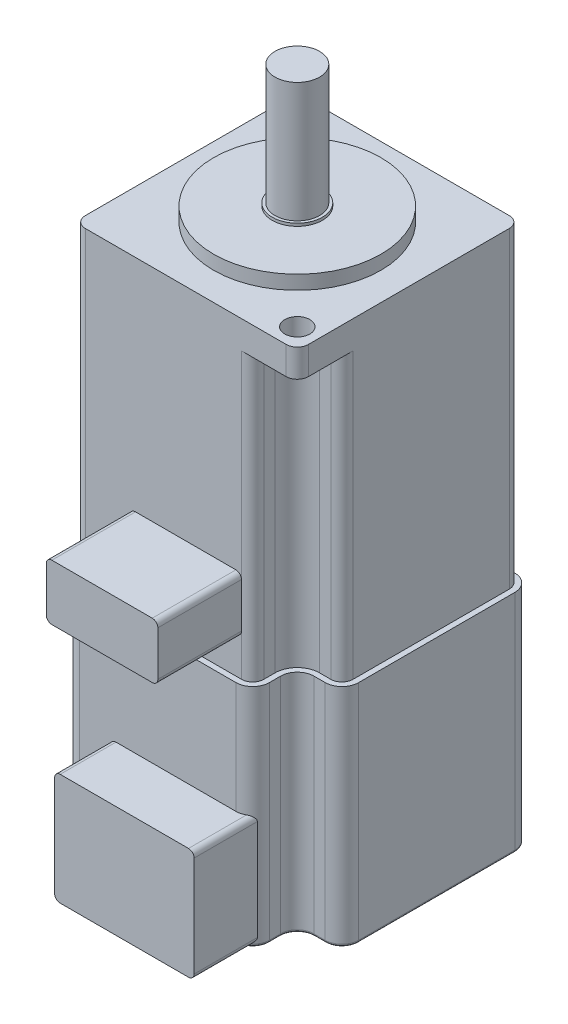
SolidWorks part; units mm, degrees
material "Ductile Iron"
ref_plane "Front Plane" through (0, 0, 0) normal (0, 0, 1) x (1, 0, 0)
ref_plane "Top Plane" through (0, 0, 0) normal (0, 1, 0) x (1, 0, 0)
ref_plane "Right Plane" through (0, 0, 0) normal (1, 0, 0) x (0, 0, -1)
sketch "Sketch1" plane through (0, 0, 0) normal (0, 1, 0) x (1, 0, 0)
  line L1 (2, 0) -> (38, 0)
  line L2 (0, 2) -> (0, 38)
  line L3 (2, 40) -> (38, 40)
  line L4 (40, 2) -> (40, 38)
  arc A0 (40, 38) -> (38, 40) centre (38, 38) ccw
  arc A1 (38, 0) -> (40, 2) centre (38, 2) ccw
  arc A2 (0, 2) -> (2, 0) centre (2, 2) ccw
  arc A3 (2, 40) -> (0, 38) centre (2, 38) ccw
  point P11 (0, 0)
  point P14 (0, 40)
  dimension "D2" = 2
  dimension "D1" = 40
extrude "Boss-Extrude1" add sketch "Sketch1" along normal blind 5
sketch "Sketch2" plane through (0, 5, 0) normal (0, 1, 0) x (1, 0, 0)
  line L0 (38, 40) -> (2, 40) construction
  line L1 (0, 38) -> (0, 2) construction
  circle A0 centre (20, 20) radius 15
  point P0 (20, 40)
  point P1 (0, 20)
  dimension "D1" = 30
extrude "Boss-Extrude2" add sketch "Sketch2" along normal blind 2.5
sketch "Sketch3" plane through (0, 5, 0) normal (0, 1, 0) x (1, 0, 0)
  line L0 (0.5858, 39.4142) -> (39.4142, 0.5858) construction
  circle A0 centre (20, 20) radius 23
  arc A1 (2, 40) -> (0, 38) centre (2, 38) ccw construction
  arc A2 (38, 0) -> (40, 2) centre (38, 2) ccw construction
  circle A3 centre (3.7365, 36.2635) radius 2.25
  circle A4 centre (36.2635, 3.7365) radius 2.25
  dimension "D1" = 46
  dimension "D2" = 4.5
  dimension "D3" = 4.5
extrude "Cut-Extrude1" cut sketch "Sketch3" against normal up to surface (5 mm away) contours A4 | A3 up to face at (20, 0, -20)
sketch "Sketch4" plane through (0, 0, 0) normal (0, -1, 0) x (1, 0, 0)
  line L0 (32, -2) -> (32, -4)
  line L1 (2, 0) -> (30, 0)
  line L2 (0, -2) -> (0, -30)
  line L3 (10, -40) -> (38, -40)
  line L4 (40, -10) -> (40, -38)
  line L5 (36, -8) -> (38, -8)
  line L6 (40, -2) -> (40, -38) construction
  line L7 (2, -32) -> (4, -32)
  line L8 (8, -36) -> (8, -38)
  arc A0 (40, -38) -> (38, -40) centre (38, -38) cw
  arc A1 (2, 0) -> (0, -2) centre (2, -2) ccw
  arc A2 (10, -40) -> (8, -38) centre (10, -38) cw
  arc A3 (2, -32) -> (0, -30) centre (2, -30) cw
  arc A4 (40, -10) -> (38, -8) centre (38, -10) ccw
  arc A5 (32, -2) -> (30, 0) centre (30, -2) ccw
  arc A6 (36, -8) -> (32, -4) centre (36, -4) cw
  arc A7 (4, -32) -> (8, -36) centre (4, -36) cw
  point P9 (0, 0)
  point P18 (8, -40)
  point P21 (0, -32)
  point P24 (40, -8)
  point P27 (32, 0)
  point P30 (32, -8)
  point P33 (8, -32)
  dimension "D2" = 2
  dimension "D1" = 2
  dimension "D7" = 4
  dimension "D3" = 8
  dimension "D4" = 8
  dimension "D5" = 8
  dimension "D6" = 8
extrude "Boss-Extrude3" add sketch "Sketch4" along normal blind 51
sketch "Sketch5" plane through (0, -51, 0) normal (0, -1, 0) x (1, 0, 0)
  line L16 (10, -41) -> (38, -41)
  line L17 (41, -38) -> (41, -10)
  line L18 (38, -7) -> (36, -7)
  line L19 (33, -4) -> (33, -2)
  line L20 (30, 1) -> (2, 1)
  line L21 (-1, -2) -> (-1, -30)
  line L22 (2, -33) -> (4, -33)
  line L23 (7, -36) -> (7, -38)
  line L24 (10, -41) -> (38, -41)
  line L25 (41, -38) -> (41, -10)
  line L26 (38, -7) -> (36, -7)
  line L27 (33, -4) -> (33, -2)
  line L28 (30, 1) -> (2, 1)
  line L29 (-1, -2) -> (-1, -30)
  line L30 (2, -33) -> (4, -33)
  line L31 (7, -36) -> (7, -38)
  arc A16 (7, -38) -> (10, -41) centre (10, -38) ccw
  arc A17 (38, -41) -> (41, -38) centre (38, -38) ccw
  arc A18 (41, -10) -> (38, -7) centre (38, -10) ccw
  arc A19 (33, -4) -> (36, -7) centre (36, -4) ccw
  arc A20 (33, -2) -> (30, 1) centre (30, -2) ccw
  arc A21 (2, 1) -> (-1, -2) centre (2, -2) ccw
  arc A22 (-1, -30) -> (2, -33) centre (2, -30) ccw
  arc A23 (7, -36) -> (4, -33) centre (4, -36) ccw
  arc A24 (7, -38) -> (10, -41) centre (10, -38) ccw
  arc A25 (38, -41) -> (41, -38) centre (38, -38) ccw
  arc A26 (41, -10) -> (38, -7) centre (38, -10) ccw
  arc A27 (33, -4) -> (36, -7) centre (36, -4) ccw
  arc A28 (33, -2) -> (30, 1) centre (30, -2) ccw
  arc A29 (2, 1) -> (-1, -2) centre (2, -2) ccw
  arc A30 (-1, -30) -> (2, -33) centre (2, -30) ccw
  arc A31 (7, -36) -> (4, -33) centre (4, -36) ccw
  dimension "D1" = 1
extrude "Boss-Extrude4" add sketch "Sketch5" along normal blind 40.5
sketch "Sketch6" plane through (0, 7.5, 0) normal (0, 1, 0) x (1, 0, 0)
  circle A0 centre (20, 20) radius 4.5
  dimension "D1" = 9
extrude "Boss-Extrude5" add sketch "Sketch6" along normal blind 0.5
sketch "Sketch7" plane through (0, 8, 0) normal (0, 1, 0) x (1, 0, 0)
  circle A0 centre (20, 20) radius 4
  dimension "D1" = 8
extrude "Boss-Extrude6" add sketch "Sketch7" along normal blind 21.5
fillet "Fillet1" radius 0.5 16 edges at (7, -91.5, -37) (6.1213, -91.5, -33.8787) (3, -91.5, -33) (-0.1213, -91.5, -32.1213) (-1, -91.5, -16) (-0.1213, -91.5, 0.1213) (16, -91.5, 1) (32.1213, -91.5, 0.1213) (33, -91.5, -3) (33.8787, -91.5, -6.1213) (37, -91.5, -7) (40.1213, -91.5, -7.8787) (41, -91.5, -24) (40.1213, -91.5, -40.1213) (24, -91.5, -41) (7.8787, -91.5, -40.1213)
sketch "Sketch8" plane through (0, 0, 0) normal (0, 0, 1) x (1, 0, 0)
  line L0 (20, 5) -> (20, -159.8867) construction
  line L1 (2, 5) -> (38, 5) construction
  line L3 (11, -34.5) -> (29, -34.5)
  line L4 (10, -35.5) -> (10, -43.5)
  line L5 (11, -44.5) -> (29, -44.5)
  line L6 (30, -35.5) -> (30, -43.5)
  arc A0 (30, -35.5) -> (29, -34.5) centre (29, -35.5) ccw
  arc A1 (30, -43.5) -> (29, -44.5) centre (29, -43.5) cw
  arc A2 (11, -44.5) -> (10, -43.5) centre (11, -43.5) cw
  arc A3 (11, -34.5) -> (10, -35.5) centre (11, -35.5) ccw
  point P10 (30, -34.5)
  point P15 (10, -44.5)
  point P18 (10, -34.5)
  dimension "D5" = 1
  dimension "D1" = 10
  dimension "D2" = 20
  dimension "D3" = 10
  dimension "D4" = 39.5
extrude "Boss-Extrude7" add sketch "Sketch8" along normal blind 15 contours L3 A0 L6 A1 L5 A2 L4 A3
sketch "Sketch9" plane through (0, 0, 1) normal (0, 0, 1) x (1, 0, 0)
  line L0 (20, 5) -> (20, -101.3936) construction
  line L1 (2, 5) -> (38, 5) construction
  line L2 (2, -91) -> (30, -91) construction
  line L3 (8.5, -71) -> (31.5, -71)
  line L4 (7.5, -72) -> (7.5, -90)
  line L5 (8.5, -91) -> (31.5, -91)
  line L6 (32.5, -72) -> (32.5, -90)
  arc A0 (8.5, -91) -> (7.5, -90) centre (8.5, -90) cw
  arc A1 (32.5, -90) -> (31.5, -91) centre (31.5, -90) cw
  arc A2 (32.5, -72) -> (31.5, -71) centre (31.5, -72) ccw
  arc A3 (8.5, -71) -> (7.5, -72) centre (8.5, -72) ccw
  point P12 (7.5, -91)
  point P17 (32.5, -71)
  point P20 (7.5, -71)
  dimension "D5" = 1
  dimension "D1" = 20
  dimension "D2" = 25
  dimension "D3" = 12.5
  dimension "D4" = 0
extrude "Boss-Extrude8" add sketch "Sketch9" along normal blind 10 and the other way up to surface other way up to face at (31.8107, -71, -0.1893)
